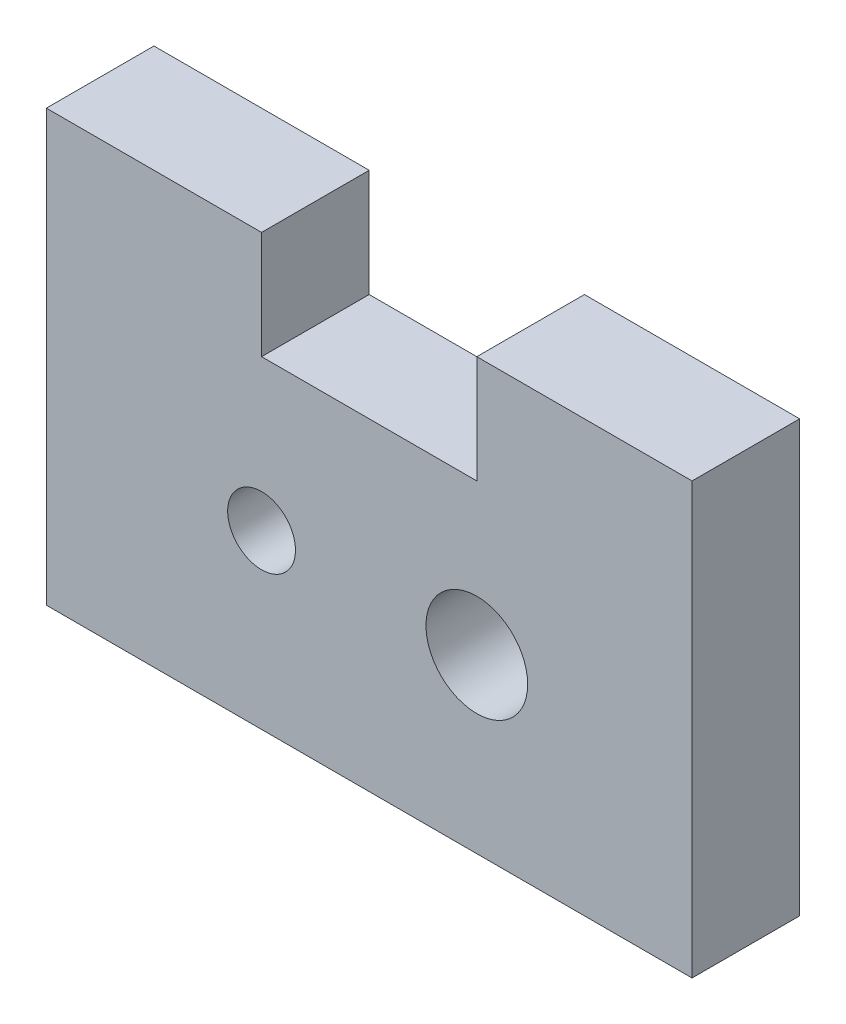
SolidWorks part; units mm, degrees
ref_plane "Front Plane" through (0, 0, 0) normal (0, 0, 1) x (1, 0, 0)
ref_plane "Top Plane" through (0, 0, 0) normal (0, 1, 0) x (1, 0, 0)
ref_plane "Right Plane" through (0, 0, 0) normal (1, 0, 0) x (0, 0, -1)
sketch "Sketch1" plane through (0, 0, 0) normal (0, 0, 1) x (1, 0, 0)
  line L0 (6.35, 12.7) -> (6.35, 9.525)
  line L1 (0, 0) -> (19.05, 0)
  line L2 (0, 0) -> (0, 12.7)
  line L3 (0, 12.7) -> (6.35, 12.7)
  line L4 (19.05, 0) -> (19.05, 12.7)
  line L5 (6.35, 9.525) -> (12.7, 9.525)
  line L6 (12.7, 9.525) -> (12.7, 12.7)
  line L7 (12.7, 12.7) -> (19.05, 12.7)
  line L8 (0, 5.08) -> (19.05, 5.08) construction
  circle A0 centre (12.7, 5.08) radius 1.5
  circle A1 centre (6.35, 5.08) radius 1
  dimension "D7" = 3
  dimension "D8" = 2
  dimension "D10" = 6.35
  dimension "D1" = 19.05
  dimension "D2" = 6.35
  dimension "D3" = 6.35
  dimension "D4" = 12.7
  dimension "D5" = 3.175
  dimension "D6" = 5.08
  dimension "D9" = 6.35
extrude "Boss-Extrude1" add sketch "Sketch1" along normal blind 3.175
